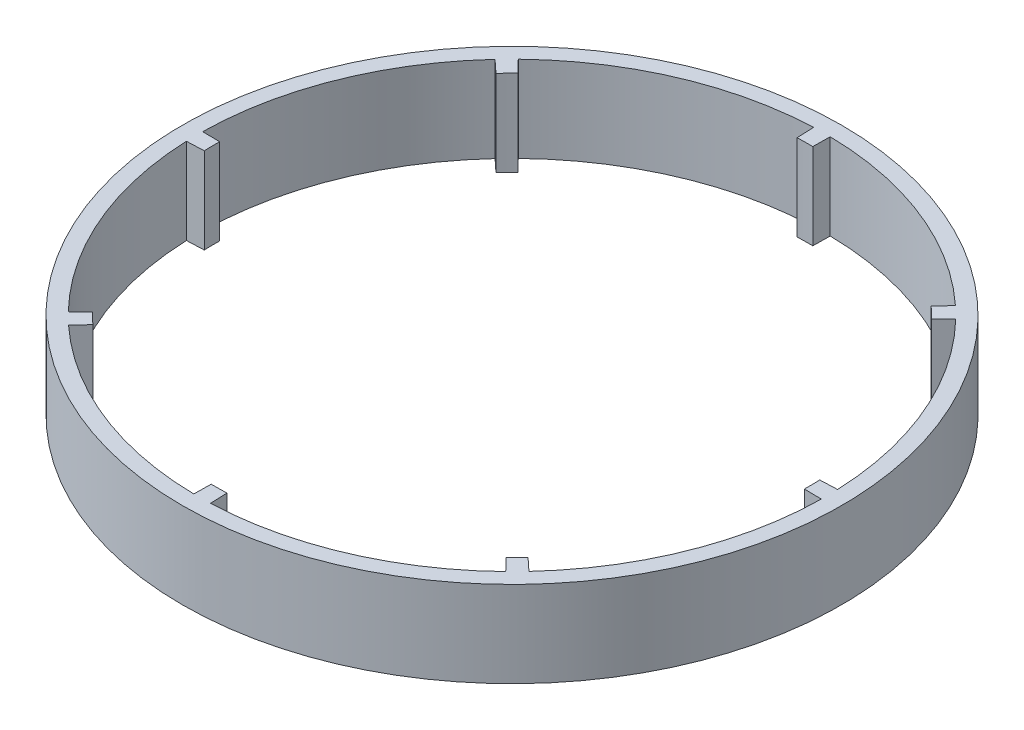
SolidWorks part; units mm, degrees
ref_plane "Front Plane" through (0, 0, 0) normal (0, 0, 1) x (1, 0, 0)
ref_plane "Top Plane" through (0, 0, 0) normal (0, 1, 0) x (1, 0, 0)
ref_plane "Right Plane" through (0, 0, 0) normal (1, 0, 0) x (0, 0, -1)
sketch "Sketch1" plane through (0, 0, 0) normal (0, 1, 0) x (1, 0, 0)
  line L0 (1.4632, 103.4897) -> (1.548, 109.4891)
  line L1 (-3.955, 103.4244) -> (-4.1843, 109.42)
  line L2 (74.2129, 72.1436) -> (78.5151, 76.3258)
  line L3 (70.3355, 75.9287) -> (74.4129, 80.3304)
  line L4 (103.4897, -1.4632) -> (109.4891, -1.548)
  line L5 (103.4244, 3.955) -> (109.42, 4.1843)
  line L6 (72.1436, -74.2129) -> (76.3258, -78.5151)
  line L7 (75.9287, -70.3355) -> (80.3304, -74.4129)
  line L8 (-1.4632, -103.4897) -> (-1.548, -109.4891)
  line L9 (3.955, -103.4244) -> (4.1843, -109.42)
  line L10 (-74.2129, -72.1436) -> (-78.5151, -76.3258)
  line L11 (-70.3355, -75.9287) -> (-74.4129, -80.3304)
  line L12 (-103.4897, 1.4632) -> (-109.4891, 1.548)
  line L13 (-103.4244, -3.955) -> (-109.42, -4.1843)
  line L14 (-72.1436, 74.2129) -> (-76.3258, 78.5151)
  line L15 (-75.9287, 70.3355) -> (-80.3304, 74.4129)
  circle A0 centre (0, 0) radius 115
  arc A1 (-4.1843, 109.42) -> (-76.3258, 78.5151) centre (0, 0) ccw
  arc A3 (-80.3304, 74.4129) -> (-109.4891, 1.548) centre (0, 0) ccw
  arc A4 (-109.42, -4.1843) -> (-78.5151, -76.3258) centre (0, 0) ccw
  arc A5 (-74.4129, -80.3304) -> (-1.548, -109.4891) centre (0, 0) ccw
  arc A6 (4.1843, -109.42) -> (76.3258, -78.5151) centre (0, 0) ccw
  arc A7 (80.3304, -74.4129) -> (109.4891, -1.548) centre (0, 0) ccw
  arc A8 (109.42, 4.1843) -> (78.5151, 76.3258) centre (0, 0) ccw
  arc A9 (74.4129, 80.3304) -> (1.548, 109.4891) centre (0, 0) ccw
  circle A10 centre (0, 0) radius 103.5
  point P38 (0, 0)
  dimension "D1" = 219
  dimension "D2" = 230
  dimension "D3" = 207
  dimension "D4" = 3
  dimension "D5" = 8
extrude "Boss-Extrude1" add sketch "Sketch1" along normal blind 30 contours A0 A10 L6 A6 L9 L8 A5 L11 L10 A4 L13 L12 A3 L15 L14 A1 L1 L0 A9 L3 L2 A8 L5 L4 A7 L7
